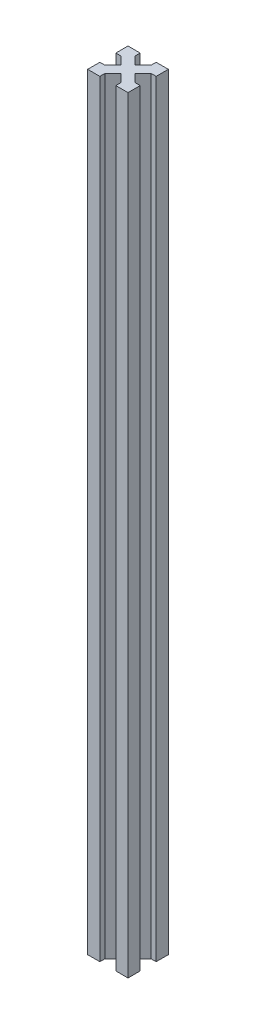
SolidWorks part; units mm, degrees
ref_plane "Plan de face" through (0, 0, 0) normal (0, 0, 1) x (1, 0, 0)
ref_plane "Plan de dessus" through (0, 0, 0) normal (0, 1, 0) x (1, 0, 0)
ref_plane "Plan de droite" through (0, 0, 0) normal (1, 0, 0) x (0, 0, -1)
sketch "Esquisse1" plane through (0, 0, 0) normal (0, 1, 0) x (1, 0, 0)
  line L0 (-2.5, 17.5) -> (-17.5, 17.5)
  line L1 (0, 0) -> (-20, 0)
  line L2 (0, 0) -> (0, 20)
  line L3 (0, 20) -> (-20, 20)
  line L4 (-20, 0) -> (-20, 20)
  line L5 (0, 20) -> (-20, 0) construction
  line L6 (-17.5, 2.5) -> (-17.5, 17.5)
  line L11 (-2.5, 2.5) -> (-17.5, 2.5)
  line L12 (-2.5, 2.5) -> (-2.5, 17.5)
  line L13 (-20, 20) -> (0, 0) construction
  line L14 (-26.9957, 23.4601) -> (-23.4601, 26.9957)
  line L15 (-26.9957, 23.4601) -> (3.4601, -6.9957)
  line L16 (-23.4601, 26.9957) -> (6.9957, -3.4601)
  line L17 (3.4601, -6.9957) -> (6.9957, -3.4601)
  line L18 (-26.9957, 23.4601) -> (6.9957, -3.4601) construction
  line L19 (-23.4601, 26.9957) -> (3.4601, -6.9957) construction
  line L20 (-10, 20) -> (-10, 0) construction
  line L21 (-23.4601, -6.9957) -> (-26.9957, -3.4601)
  line L22 (3.4601, 26.9957) -> (-26.9957, -3.4601)
  line L23 (6.9957, 23.4601) -> (-23.4601, -6.9957)
  line L24 (6.9957, 23.4601) -> (3.4601, 26.9957)
  line L25 (-17.5, 13.9645) -> (-20, 13.9645)
  line L26 (-20, 10) -> (0, 10) construction
  line L27 (-17.5, 6.0355) -> (-20, 6.0355)
  line L28 (-2.5, 6.0355) -> (0, 6.0355)
  line L29 (-2.5, 13.9645) -> (0, 13.9645)
  line L30 (-2.5, 6.0355) -> (0, 6.0355)
  line L31 (-2.5, 13.9645) -> (0, 13.9645)
  line L32 (-13.9645, 2.5) -> (-13.9645, 0)
  line L33 (-6.0355, 17.5) -> (-6.0355, 20)
  line L34 (-13.9645, 17.5) -> (-13.9645, 20)
  line L35 (-6.0355, 2.5) -> (-6.0355, 0)
  point P11 (-10, 10)
  dimension "D1" = 20
  dimension "D2" = 20
  dimension "D3" = 7.3934
  dimension "D4" = 2.5
  dimension "D5" = 43.071
  dimension "D6" = 2.5
extrude "Boss.-Extru.1" add sketch "Esquisse1" along normal blind 380 contours L15 L35 L1 | L16 L12 L11 L15 L1 L2 | L28 L16 L2 | L16 L23 L15 L11 L12 | L32 L23 L1 | L23 L11 L6 L22 L4 L1 | L22 L27 L4 | L23 L15 L22 L6 L11 | L23 L16 L22 L15 | L23 L12 L0 L22 L16 | L23 L2 L3 L22 L0 L12 | L23 L29 L2 | L33 L22 L3 | L16 L34 L3 | L16 L3 L4 L15 L6 L0 | L25 L15 L4 | L22 L16 L0 L6 L15
